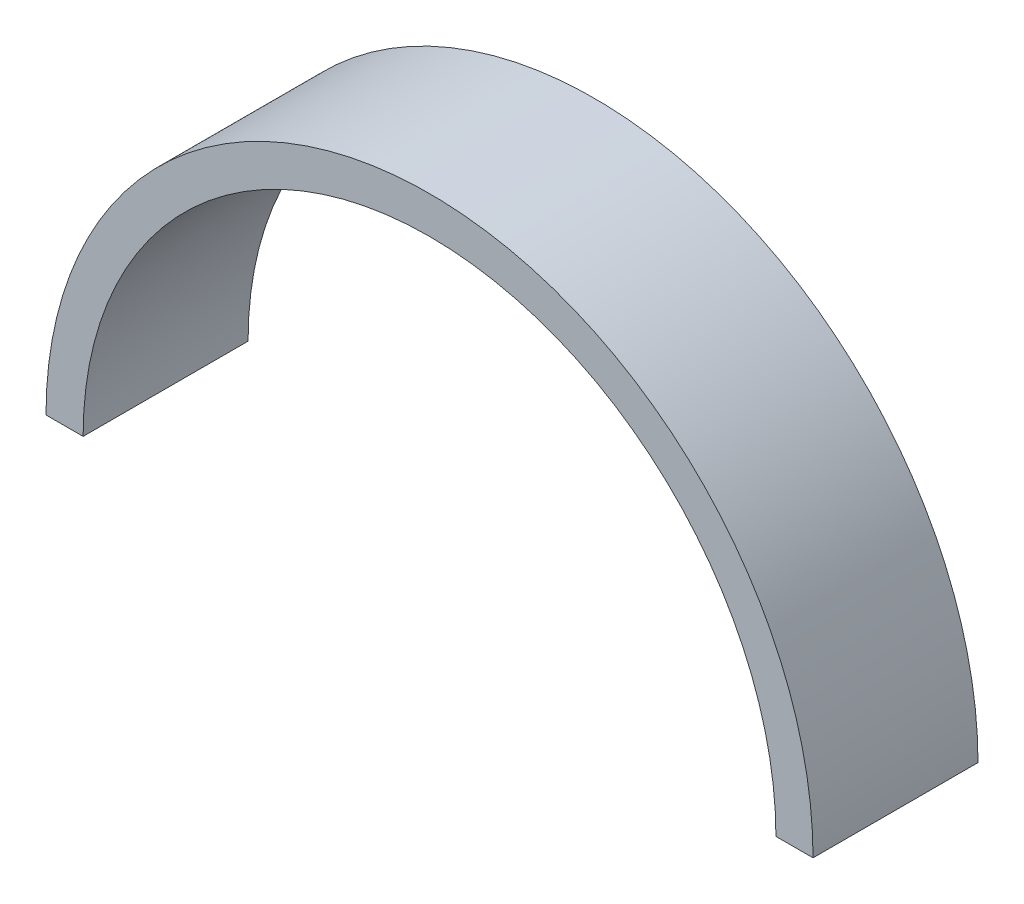
SolidWorks part; units mm, degrees
ref_plane "Front" through (0, 0, 0) normal (0, 0, 1) x (1, 0, 0)
ref_plane "Top" through (0, 0, 0) normal (0, 1, 0) x (1, 0, 0)
ref_plane "Right" through (0, 0, 0) normal (1, 0, 0) x (0, 0, -1)
sketch "草图1" plane through (0, 0, 0) normal (0, 0, 1) x (1, 0, 0)
  line L0 (28.0398, 0) -> (82.9075, 0) construction
  line L1 (-46.5, 0) -> (-42, 0)
  line L2 (42, 0) -> (46.5, 0)
  arc A0 (-46.5, 0) -> (46.5, 0) centre (0, 0) cw
  arc A1 (-42, 0) -> (42, 0) centre (0, 0) cw
extrude "凸台-拉伸1" add sketch "草图1" along normal blind 20
